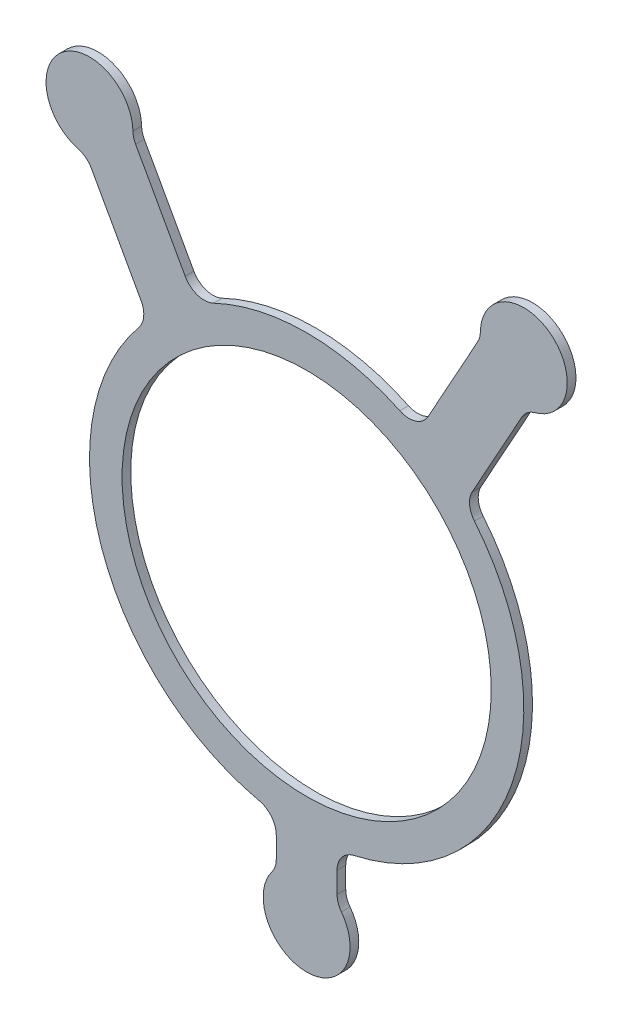
SolidWorks part; units mm, degrees
ref_plane "Front" through (0, 0, 0) normal (0, 0, 1) x (1, 0, 0)
ref_plane "Top" through (0, 0, 0) normal (0, 1, 0) x (1, 0, 0)
ref_plane "Right" through (0, 0, 0) normal (1, 0, 0) x (0, 0, -1)
sketch "Sketch1" plane through (0, 0, 0) normal (0, 0, 1) x (1, 0, 0)
  line L0 (0, 0) -> (0, 85.725) construction
  line L7 (50.0087, 171.9238) -> (35.5122, 145.7484)
  line L8 (62.9177, 159.3119) -> (48.4212, 133.1364)
  line L9 (-62.9177, 159.3119) -> (-48.4212, 133.1364)
  line L10 (-50.0087, 171.9238) -> (-35.5122, 145.7484)
  line L13 (8.89, 11.43) -> (8.89, 17.5578)
  line L14 (-8.89, 11.43) -> (-8.89, 17.5578)
  arc A0 (-50.8025, 174.8752) -> (-66.8151, 162.3653) centre (-63.5, 174.625) ccw
  arc A1 (50.8025, 174.8752) -> (66.8151, 162.3653) centre (63.5, 174.625) cw
  arc A2 (-10.16, 7.62) -> (10.16, 7.62) centre (0, 0) ccw
  arc A3 (-49.0693, 126.0295) -> (-13.8545, 23.7548) centre (0, 85.725) ccw
  arc A4 (27.2338, 143.0885) -> (-27.2338, 143.0885) centre (0, 85.725) ccw
  arc A5 (13.8545, 23.7548) -> (49.0693, 126.0295) centre (0, 85.725) ccw
  circle A6 centre (0, 85.725) radius 53.975
  arc A7 (-48.4212, 133.1364) -> (-49.0693, 126.0295) centre (-53.9762, 130.06) cw
  arc A8 (-27.2338, 143.0885) -> (-35.5122, 145.7484) centre (-29.9572, 148.8248) cw
  arc A9 (35.5122, 145.7484) -> (27.2338, 143.0885) centre (29.9572, 148.8248) cw
  arc A10 (49.0693, 126.0295) -> (48.4212, 133.1364) centre (53.9762, 130.06) cw
  arc A11 (8.89, 17.5578) -> (13.8545, 23.7548) centre (15.24, 17.5578) cw
  arc A12 (-13.8545, 23.7548) -> (-8.89, 17.5578) centre (-15.24, 17.5578) cw
  arc A13 (-66.8151, 162.3653) -> (-62.9177, 159.3119) centre (-68.4727, 156.2355) cw
  arc A14 (-50.0087, 171.9238) -> (-50.8025, 174.8752) centre (-44.4537, 175.0003) cw
  arc A15 (50.0087, 171.9238) -> (50.8025, 174.8752) centre (44.4537, 175.0003) ccw
  arc A16 (62.9177, 159.3119) -> (66.8151, 162.3653) centre (68.4727, 156.2355) cw
  arc A17 (10.16, 7.62) -> (8.89, 11.43) centre (15.24, 11.43) cw
  arc A18 (-8.89, 11.43) -> (-10.16, 7.62) centre (-15.24, 11.43) cw
  point P8 (0, 182.88)
  point P20 (32.4868, 140.2856)
  point P27 (8.89, 22.8504)
  dimension "D3" = 25.4
  dimension "D4" = 25.4
  dimension "D12" = 127
  dimension "D2" = 107.95
  dimension "D5" = 6.35
  dimension "D6" = 85.725
  dimension "D7" = 88.9
  dimension "D10" = 8.89
  dimension "D11" = 8.89
extrude "Base-Extrude" add sketch "Sketch1" along normal blind 2.54
